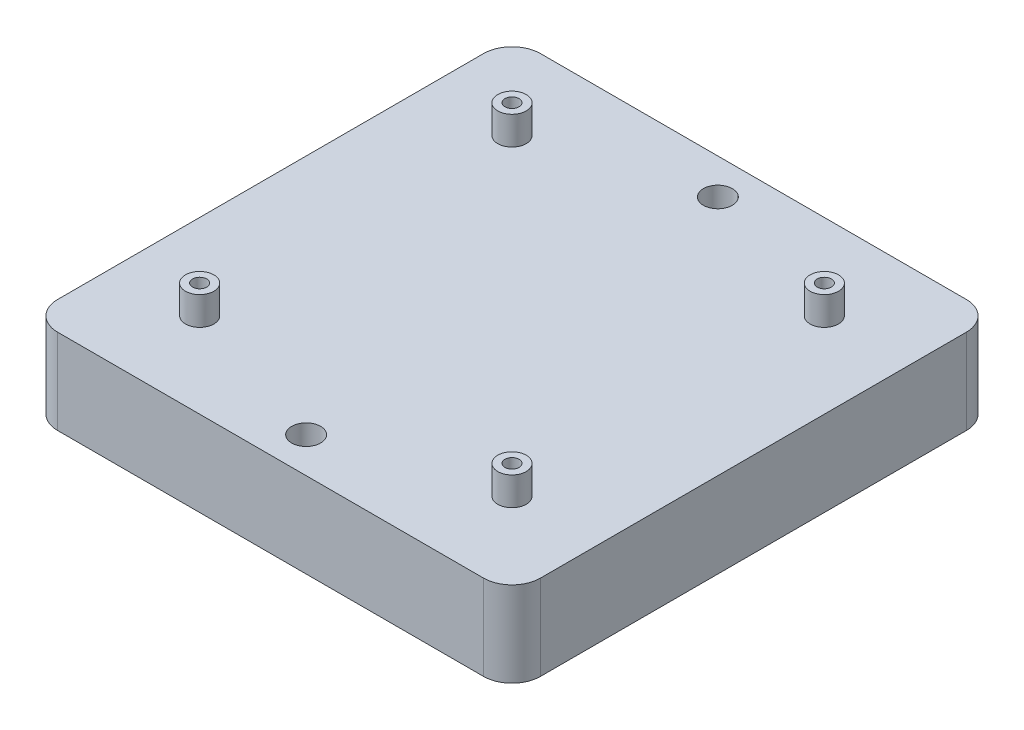
SolidWorks part; units mm, degrees
ref_plane "Front Plane" through (0, 0, 0) normal (0, 0, 1) x (1, 0, 0)
ref_plane "Top Plane" through (0, 0, 0) normal (0, 1, 0) x (1, 0, 0)
ref_plane "Right Plane" through (0, 0, 0) normal (1, 0, 0) x (0, 0, -1)
sketch "Sketch1" plane through (0, 0, 0) normal (0, 1, 0) x (1, 0, 0)
  line L0 (25, 25) -> (25, 145) construction
  line L9 (0, 0) -> (170, 0)
  line L10 (0, 0) -> (0, 170)
  line L11 (0, 170) -> (170, 170)
  line L12 (170, 0) -> (170, 170)
  line L13 (25, 145) -> (145, 145) construction
  line L14 (145, 25) -> (145, 145) construction
  line L15 (25, 25) -> (145, 25) construction
  line L16 (85, 25) -> (85, 0) construction
  line L17 (85, 145) -> (85, 170) construction
  circle A3 centre (85, 12.5) radius 5.1 construction
  circle A4 centre (85, 157.5) radius 5.1 construction
  dimension "D3" = 25
  dimension "D1" = 170
  dimension "D2" = 170
extrude "Boss-Extrude2" add sketch "Sketch1" along normal blind 30
sketch "Sketch2" plane through (0, 30, 0) normal (0, 1, 0) x (1, 0, 0)
  line L4 (85, 25) -> (85, 0) construction
  line L5 (0, 0) -> (170, 0) construction
  line L6 (85, 145) -> (85, 170) construction
  line L7 (170, 170) -> (0, 170) construction
  line L8 (25, 145) -> (25, 25)
  line L9 (25, 25) -> (145, 25)
  line L10 (145, 25) -> (145, 145)
  line L11 (145, 145) -> (25, 145)
  line L12 (25, 145) -> (25, 25)
  line L13 (25, 25) -> (145, 25)
  line L14 (145, 25) -> (145, 145)
  line L15 (145, 145) -> (25, 145)
  circle A0 centre (85, 12.5) radius 5.1
  circle A1 centre (85, 157.5) radius 5.1
  dimension "D1" = 25
extrude "Cut-Extrude1" cut sketch "Sketch2" against normal blind 25 contours A1 | A0
sketch "Sketch3" plane through (0, 30, 0) normal (0, 1, 0) x (1, 0, 0)
  line L4 (25, 25) -> (30, 30) construction
  line L5 (25, 145) -> (31.4254, 140)
  line L8 (25, 145) -> (25, 25)
  line L9 (25, 25) -> (145, 25)
  line L10 (145, 25) -> (145, 145)
  line L11 (145, 145) -> (25, 145)
  line L12 (25, 145) -> (25, 25) construction
  line L13 (25, 25) -> (145, 25) construction
  line L14 (145, 25) -> (145, 145) construction
  line L15 (145, 145) -> (25, 145) construction
  circle A0 centre (30, 30) radius 2.5
  circle A1 centre (30, 30) radius 5
  circle A2 centre (140, 30) radius 5
  circle A3 centre (140, 30) radius 2.5
  circle A4 centre (30, 140) radius 5
  circle A5 centre (30, 140) radius 2.5
  circle A6 centre (140, 140) radius 5
  circle A7 centre (140, 140) radius 2.5
  dimension "D4" = 5
  dimension "D5" = 10
  dimension "D2" = 5
  dimension "D3" = 7.0711
  dimension "D1" = 25
  dimension "D6" = 2
  dimension "D7" = 2
extrude "Boss-Extrude3" add sketch "Sketch3" along normal blind 10
fillet "Fillet1" radius 10 4 edges at (170, 15, 0) (170, 15, -170) (0, 15, 0) (0, 15, -170)
